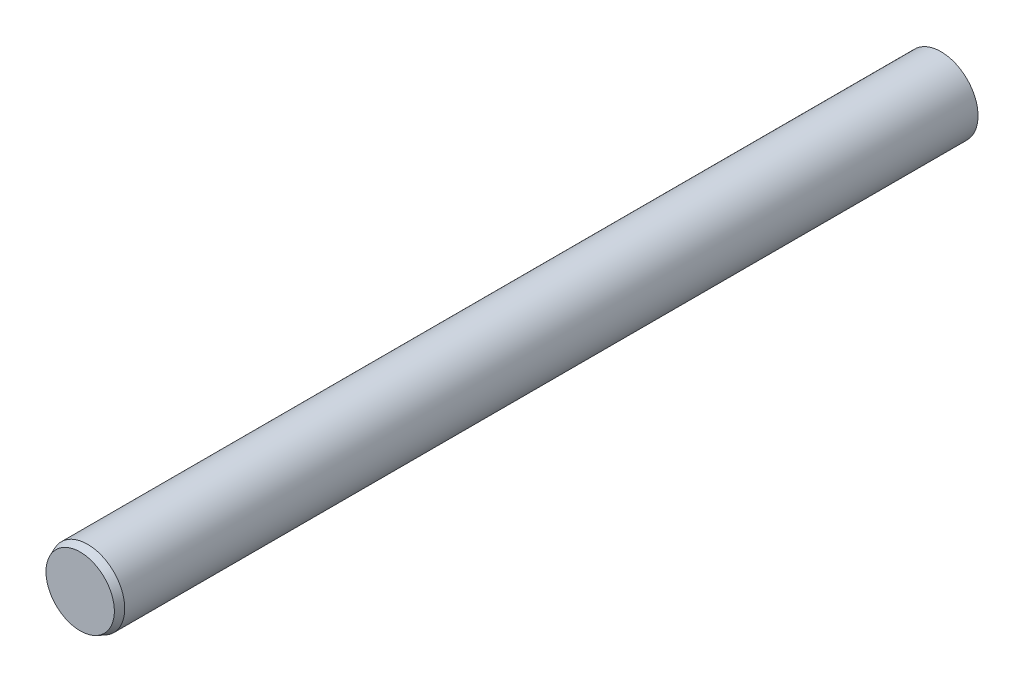
SolidWorks part; units mm, degrees
ref_plane "Front Plane" through (0, 0, 0) normal (0, 0, 1) x (1, 0, 0)
ref_plane "Top Plane" through (0, 0, 0) normal (0, 1, 0) x (1, 0, 0)
ref_plane "Right Plane" through (0, 0, 0) normal (1, 0, 0) x (0, 0, -1)
ref_plane "Plane1" through (0, 0, 0) normal (0, -1, 0) x (1, 0, 0)
sketch "Sketch1" plane through (0, 0, 0) normal (0, -1, 0) x (1, 0, 0)
  line L0 (2.3, 20.266) -> (0, 20.266)
  line L1 (0, 20.266) -> (0, -37.654)
  line L2 (0, -37.654) -> (2.5, -37.654)
  line L3 (2.5, -37.654) -> (2.5, 19.766)
  line L4 (2.5, 19.766) -> (2.3, 20.266)
  line L5 (0, 20.266) -> (0, -37.654) construction
revolve "Revolve1" add sketch "Sketch1" angle 360 about L5
